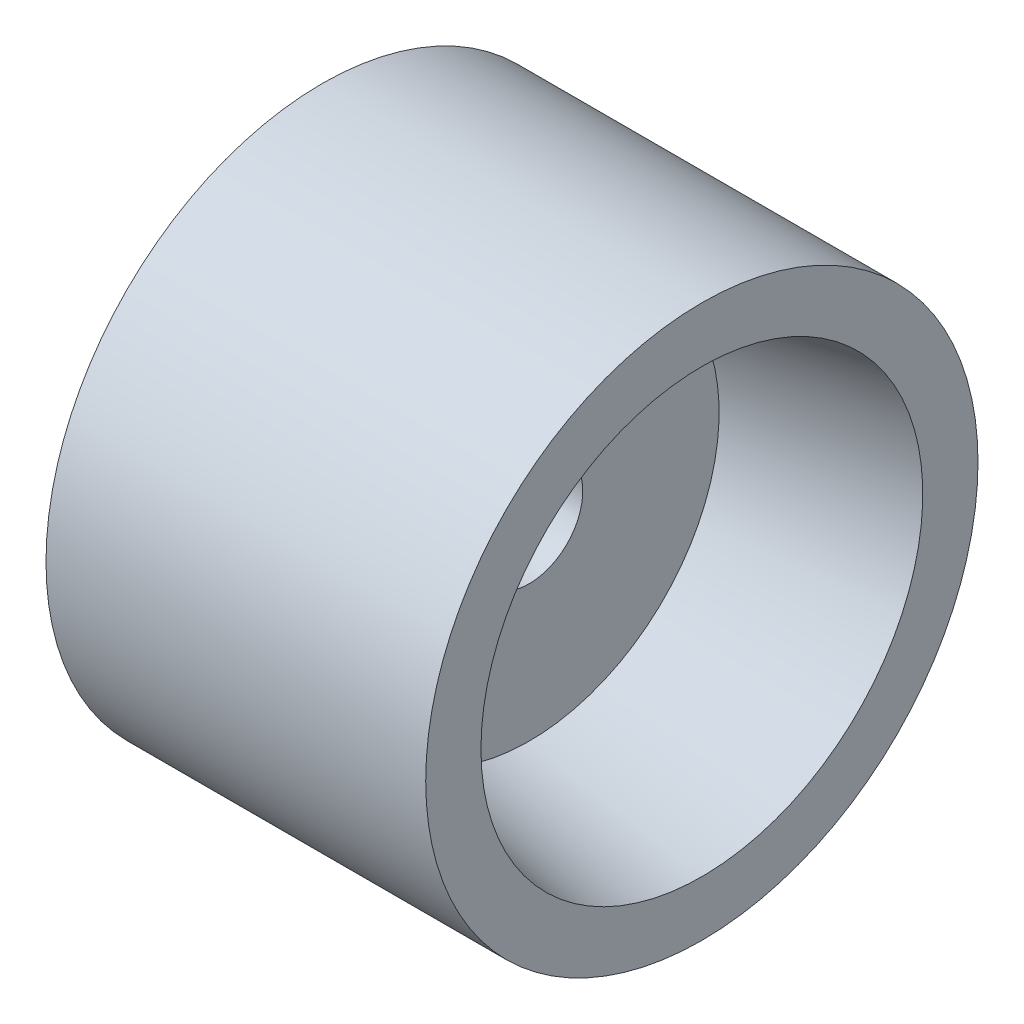
SolidWorks part; units mm, degrees
ref_plane "Ebene vorne" through (0, 0, 0) normal (0, 0, 1) x (1, 0, 0)
ref_plane "Ebene oben" through (0, 0, 0) normal (0, 1, 0) x (1, 0, 0)
ref_plane "Ebene rechts" through (0, 0, 0) normal (1, 0, 0) x (0, 0, -1)
sketch "Skizze1" plane through (0, 0, 0) normal (0, 0, 1) x (1, 0, 0)
  line L0 (0, 0) -> (33.7324, 0) construction
  line L1 (11, 1.55) -> (8, 1.55)
  line L2 (8, 1.55) -> (8, 4)
  line L3 (8, 4) -> (4, 4)
  line L4 (4, 4) -> (4, 5.5)
  line L14 (11, 5.5) -> (11, 1.55)
  line L16 (5, 8) -> (16, 8)
  line L17 (16, 8) -> (16, 6.4)
  line L18 (16, 6.4) -> (11, 5.5)
  line L19 (5, 8) -> (5, 6.4)
  line L20 (5, 6.4) -> (4, 5.5)
  point P5 (6.389, 9.3434)
  dimension "D2" = 3.1
  dimension "D3" = 8
  dimension "D4" = 4
  dimension "D5" = 1
  dimension "D6" = 12
  dimension "D7" = 16
  dimension "D8" = 1.6
  dimension "D9" = 11
  dimension "D10" = 1.6
  dimension "D12" = 3
  dimension "D13" = 11
revolve "Rotation1" add sketch "Skizze1" angle 360 about L0
